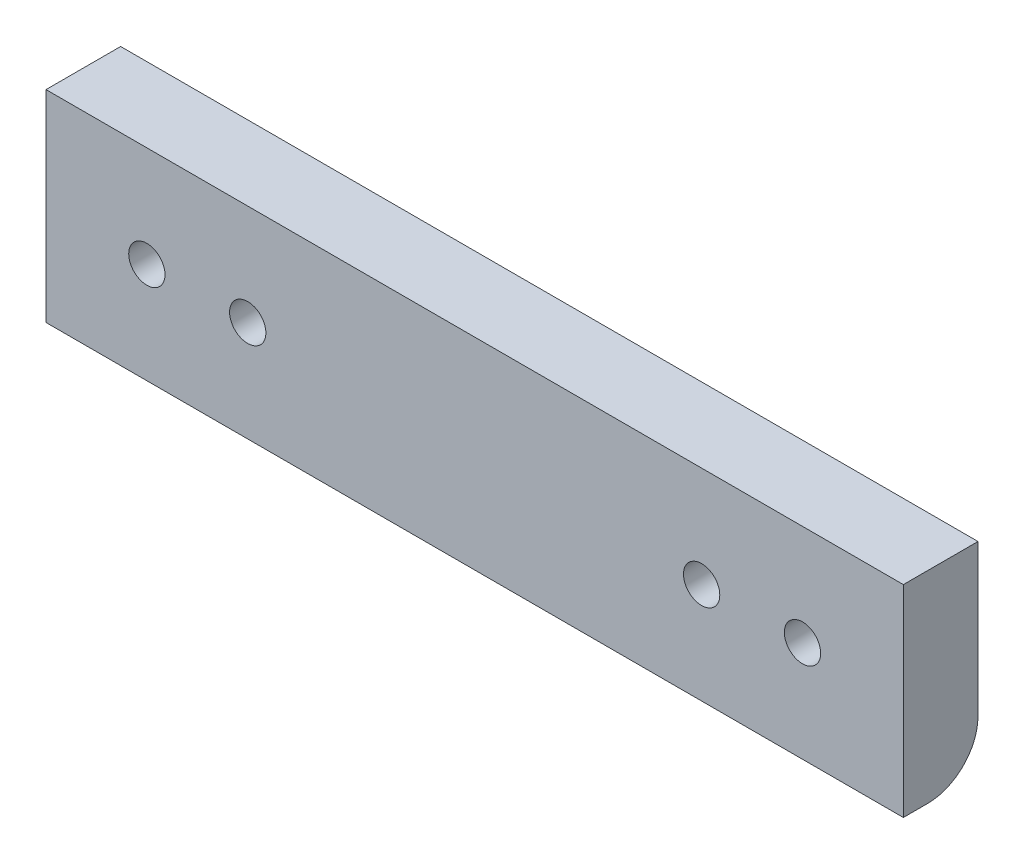
SolidWorks part; units mm, degrees
material "PEI"
ref_plane "Front Plane" through (0, 0, 0) normal (0, 0, 1) x (1, 0, 0)
ref_plane "Top Plane" through (0, 0, 0) normal (0, 1, 0) x (1, 0, 0)
ref_plane "Right Plane" through (0, 0, 0) normal (1, 0, 0) x (0, 0, -1)
sketch "Sketch1" plane through (0, 0, 0) normal (0, 0, 1) x (1, 0, 0)
  line L0 (0, 0) -> (0, 28195.5738) construction
  line L1 (42.5, -10) -> (-42.5, -10)
  line L2 (42.5, -10) -> (42.5, 10)
  line L3 (42.5, 10) -> (-42.5, 10)
  line L4 (-42.5, -10) -> (-42.5, 10)
  line L5 (42.5, -10) -> (-42.5, 10) construction
  line L6 (42.5, 10) -> (-42.5, -10) construction
  line L7 (-27.5, 1.4389) -> (-27.5, -49998.5611) construction
  circle A0 centre (-32.5, 0) radius 1.8
  circle A2 centre (-22.5, 0) radius 1.8
  circle A3 centre (32.5, 0) radius 1.8
  circle A4 centre (22.5, 0) radius 1.8
  point P0 (0, 0)
  dimension "D2" = 3.6
  dimension "D1" = 32.5
  dimension "D3" = 10
  dimension "D4" = 10
  dimension "D5" = 5
extrude "Boss-Extrude1" add sketch "Sketch1" along normal blind 7.4
sketch "Sketch2" plane through (0, 0, 0) normal (0, 0, -1) x (-1, 0, 0)
  line L0 (0, 0) -> (0, 50000) construction
  line L1 (27.5, -3.3048) -> (27.5, 49996.6952) construction
  line L2 (20.6525, -3.2) -> (18.805, 0)
  line L3 (36.195, 0) -> (34.3475, 3.2)
  line L4 (34.3475, 3.2) -> (30.6525, 3.2)
  line L5 (30.6525, 3.2) -> (28.805, 0)
  line L6 (28.805, 0) -> (30.6525, -3.2)
  line L7 (30.6525, -3.2) -> (34.3475, -3.2)
  line L8 (34.3475, -3.2) -> (36.195, 0)
  line L9 (24.3475, -3.2) -> (20.6525, -3.2)
  line L10 (26.195, 0) -> (24.3475, -3.2)
  line L11 (24.3475, 3.2) -> (26.195, 0)
  line L12 (20.6525, 3.2) -> (24.3475, 3.2)
  line L13 (18.805, 0) -> (20.6525, 3.2)
  line L14 (-18.805, 0) -> (-20.6525, 3.2)
  line L15 (-20.6525, 3.2) -> (-24.3475, 3.2)
  line L16 (-24.3475, 3.2) -> (-26.195, 0)
  line L17 (-26.195, 0) -> (-24.3475, -3.2)
  line L18 (-24.3475, -3.2) -> (-20.6525, -3.2)
  line L19 (-34.3475, -3.2) -> (-36.195, 0)
  line L20 (-30.6525, -3.2) -> (-34.3475, -3.2)
  line L21 (-28.805, 0) -> (-30.6525, -3.2)
  line L22 (-30.6525, 3.2) -> (-28.805, 0)
  line L23 (-34.3475, 3.2) -> (-30.6525, 3.2)
  line L24 (-36.195, 0) -> (-34.3475, 3.2)
  line L25 (-20.6525, -3.2) -> (-18.805, 0)
  circle A0 centre (32.5, 0) radius 3.2 construction
  circle A1 centre (22.5, 0) radius 3.2 construction
  circle A2 centre (-22.5, 0) radius 3.2 construction
  circle A3 centre (-32.5, 0) radius 3.2 construction
  dimension "D1" = 5
  dimension "D2" = 6.4
extrude "Cut-Extrude1" cut sketch "Sketch2" against normal blind 4.4
fillet "Fillet1" radius 5 1 edges at (0, -10, 0)
